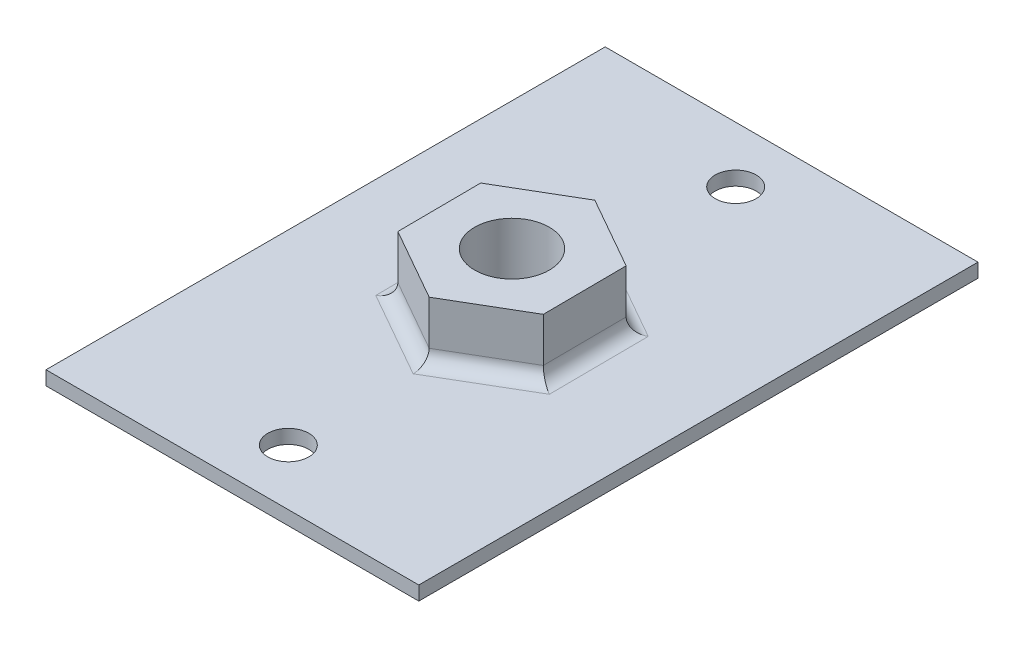
SolidWorks part; units mm, degrees
ref_plane "Front Plane" through (0, 0, 0) normal (0, 0, 1) x (1, 0, 0)
ref_plane "Top Plane" through (0, 0, 0) normal (0, 1, 0) x (1, 0, 0)
ref_plane "Right Plane" through (0, 0, 0) normal (1, 0, 0) x (0, 0, -1)
sketch "Sketch1" plane through (0, 0, 0) normal (0, 1, 0) x (1, 0, 0)
  line L1 (3.8595, 2.2639) -> (-0.0309, 4.4744)
  line L2 (-0.0309, 4.4744) -> (-3.8904, 2.2104)
  line L3 (-3.8904, 2.2104) -> (-3.8595, -2.2639)
  line L4 (-3.8595, -2.2639) -> (0.0309, -4.4744)
  line L5 (0.0309, -4.4744) -> (3.8904, -2.2104)
  line L6 (3.8904, -2.2104) -> (3.8595, 2.2639)
  circle A0 centre (0, 0) radius 3.875 construction
  circle A1 centre (0, 0) radius 2
extrude "Extrude1" add sketch "Sketch1" along normal blind 3.125
sketch "Sketch2" plane through (0, 0, 0) normal (0, -1, 0) x (1, 0, 0)
  line L0 (12.011, 0) -> (-15.6156, 0) construction
  line L2 (10, 0) -> (10, -15)
  line L3 (10, -15) -> (-10, -15)
  line L4 (-10, -15) -> (-10, 15)
  line L5 (-10, 15) -> (10, 15)
  line L6 (10, 15) -> (10, 0)
  circle A0 centre (0, -12) radius 1.1
  circle A1 centre (0, 12) radius 1.1
  dimension "D1" = 3
extrude "Extrude2" add sketch "Sketch2" along normal blind 0.75
fillet "Fillet1" radius 0.75 6 edges at (1.9143, 0, -3.3691) (-1.9606, 0, -3.3424) (-3.8749, 0, 0.0268) (-1.9143, 0, 3.3691) (1.9606, 0, 3.3424) (3.8749, 0, -0.0268)
